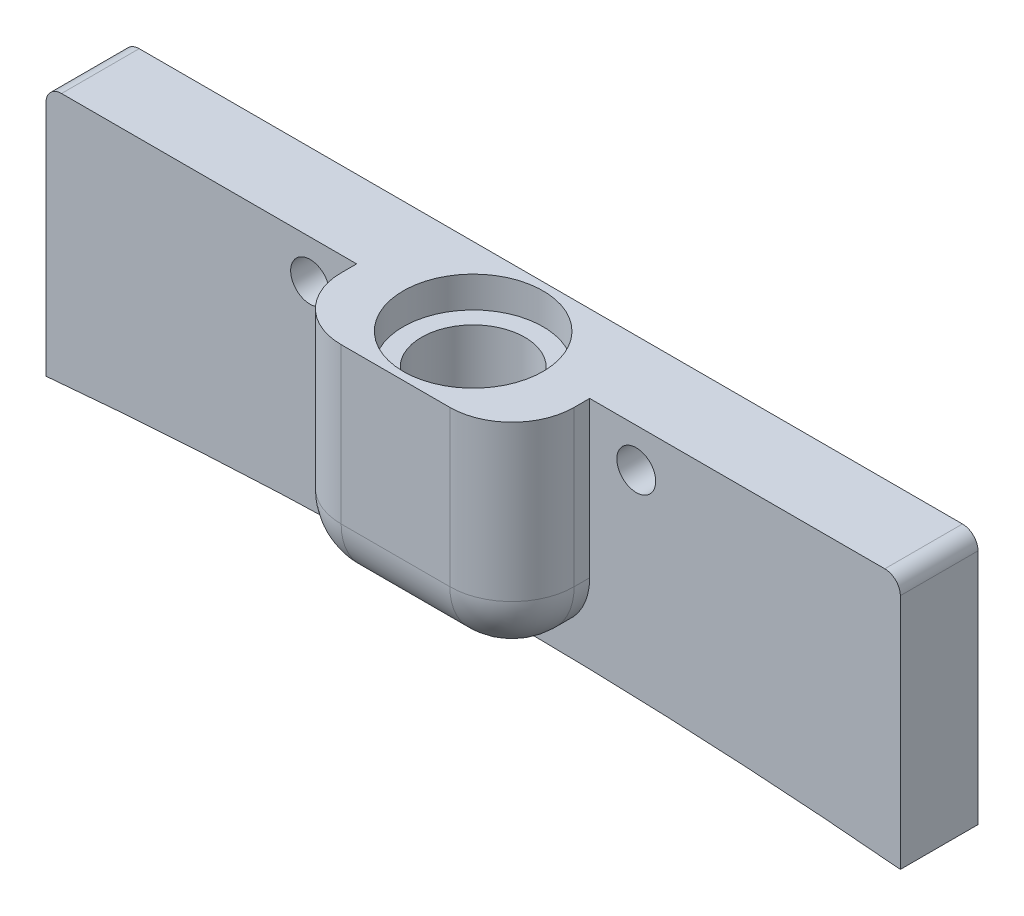
SolidWorks part; units mm, degrees
ref_plane "Front Plane" through (0, 0, 0) normal (0, 0, 1) x (1, 0, 0)
ref_plane "Top Plane" through (0, 0, 0) normal (0, 1, 0) x (1, 0, 0)
ref_plane "Right Plane" through (0, 0, 0) normal (1, 0, 0) x (0, 0, -1)
ref_plane "Plane1" through (0, 0, 0) normal (0, 0, -1) x (-1, 0, 0)
sketch "Sketch1" plane through (0, 0, 0) normal (0, 0, -1) x (-1, 0, 0)
  line L0 (27.5, -16.2631) -> (27.5, 0)
  line L1 (27.5, 0) -> (-27.5, 0)
  line L2 (-27.5, 0) -> (-27.5, -16.2631)
  arc A0 (-27.5, -16.2631) -> (27.5, -16.2631) centre (0, -315) cw
extrude "Boss-Extrude1" add sketch "Sketch1" against normal blind 5
sketch "Sketch4" plane through (0, 0, 5) normal (0, 0, 1) x (1, 0, 0)
  line L0 (7.5, 0) -> (7.5, -14)
  line L1 (7.5, -14) -> (-7.5, -14)
  line L2 (-7.5, -14) -> (-7.5, 0)
  line L3 (-7.5, 0) -> (7.5, 0)
extrude "Boss-Extrude2" add sketch "Sketch4" along normal blind 5
hole_wizard "CBORE for M6 Hex Head Bolt1" positions "Sketch6" profile "Sketch5" counterbore size "M6" standard "ANSI Metric"
sketch "Sketch6" plane through (0, 0, 0) normal (0, 1, 0) x (1, 0, 0)
  point P0 (0, -5)
sketch "Sketch5" plane through (0, 0, 5) normal (1, 0, 0) x (0, 0, 1)
  line L0 (0, 0) -> (0, 11.997)
  line L1 (0, 11.997) -> (3.3235, 10)
  line L2 (3.3235, 10) -> (3.3235, 2)
  line L3 (3.3235, 2) -> (4.5, 2)
  line L4 (4.5, 2) -> (4.5, 0)
  line L5 (4.5, 0) -> (0, 0)
  line L10 (0, 11.997) -> (-3.3235, 10) construction
  line L11 (0, -6.35) -> (0, 107.95) construction
  dimension "Hole Dia." = 6.647
  dimension "Hole Depth" = 10
  dimension "C'Bore Dia." = 9
  dimension "C'Bore Depth" = 2
  dimension "Drill Angle" = 118
fillet "Fillet1" radius 1 2 edges at (27.5, 0, 2.5) (-27.5, 0, 2.5)
fillet "Fillet2" radius 4 5 edges at (7.5, -14, 7.5) (7.5, -7, 10) (-7.5, -14, 7.5) (0, -14, 10) (-7.5, -7, 10)
hole_wizard "Tap Drill for M3x0.5 Tap1" positions "3DSketch1" profile "Sketch7" hole size "M3x0.5" standard "ANSI Metric" end condition through all
sketch3d "3DSketch1"
  line L0 (-7.5, 0, 5) -> (-7.5, -10, 5) construction
  line L1 (7.5, -10, 5) -> (7.5, 0, 5) construction
  line L2 (-26.5, 0, 5) -> (-7.5, 0, 5) construction
  point P0 (-10.5, -2.5, 5)
  point P2 (10.5, -2.5, 5)
  dimension "D1" = 3
  dimension "D2" = 3
  dimension "D3" = 2.5
sketch "Sketch7" plane through (-10.5, -2.5, 5) normal (1, 0, 0) x (0, -1, 0)
  line L0 (0, 0) -> (0, 5)
  line L1 (0, 5) -> (1.25, 5)
  line L2 (1.25, 5) -> (1.25, 0)
  line L5 (1.25, 0) -> (0, 0)
  line L11 (0, -6.35) -> (0, 107.95) construction
  dimension "Thru Hole Dia." = 2.5
  dimension "Thru Hole Depth" = 5
